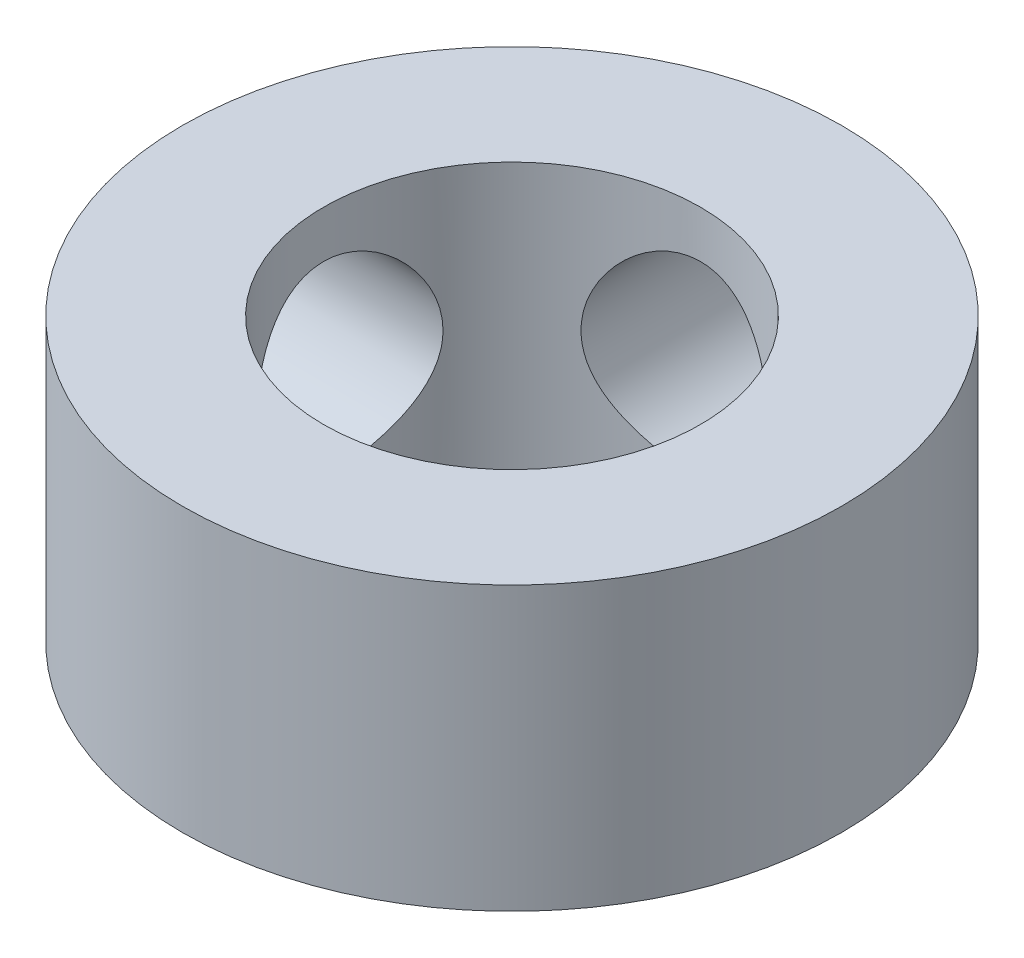
SolidWorks part; units mm, degrees
ref_plane "前视基准面" through (0, 0, 0) normal (0, 0, 1) x (1, 0, 0)
ref_plane "上视基准面" through (0, 0, 0) normal (0, 1, 0) x (1, 0, 0)
ref_plane "右视基准面" through (0, 0, 0) normal (1, 0, 0) x (0, 0, -1)
sketch "草图1" plane through (0, 0, 0) normal (0, 1, 0) x (1, 0, 0)
  circle A0 centre (0, 0) radius 7
  circle A1 centre (0, 0) radius 4
  dimension "D1" = 8
  dimension "D2" = 14
extrude "凸台-拉伸1" add sketch "草图1" along normal blind 6
sketch "草图2" plane through (0, 0, 0) normal (1, 0, 0) x (0, 0, -1)
  line L0 (-7, 0) -> (7, 0) construction
  line L1 (7, 0) -> (7, 6) construction
  circle A0 centre (0, 3) radius 2
  dimension "D1" = 4
  dimension "D2" = 3
  dimension "D3" = 7
extrude "切除-拉伸1" cut sketch "草图2" against normal blind 10
sketch "草图3" plane through (0, 0, 0) normal (0, 0, 1) x (1, 0, 0)
  line L0 (-7, 0) -> (7, 0) construction
  line L1 (7, 0) -> (7, 6) construction
  circle A0 centre (0, 3) radius 2
  dimension "D1" = 4
  dimension "D2" = 3
  dimension "D3" = 7
extrude "切除-拉伸2" cut sketch "草图3" against normal blind 10
